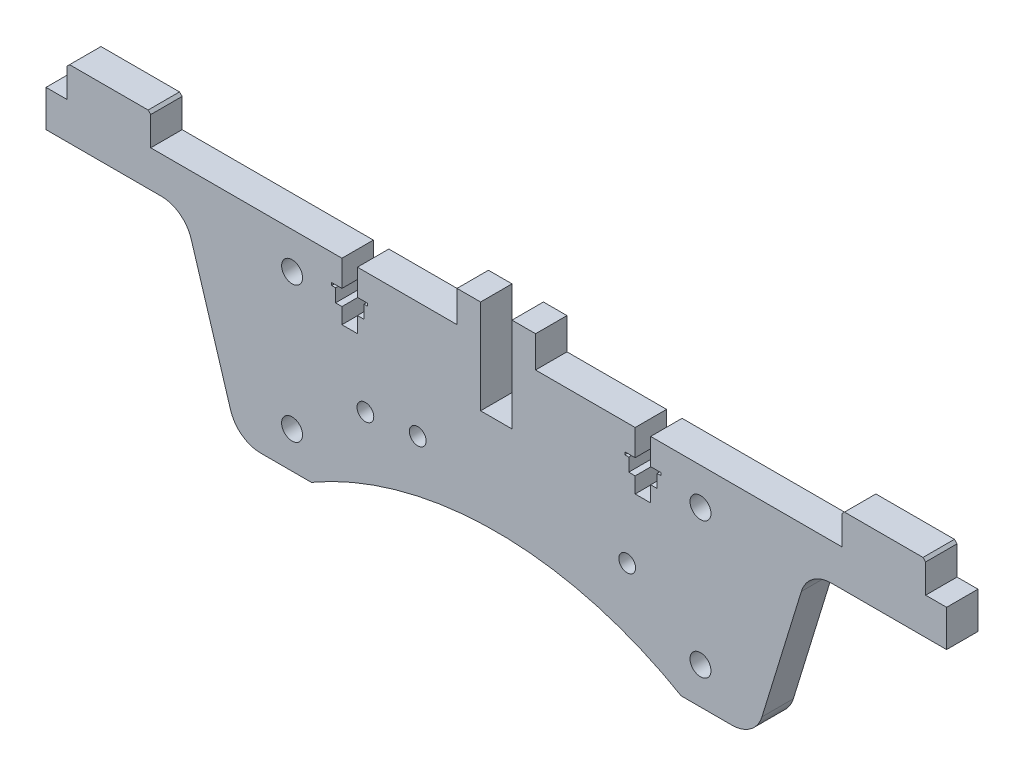
SolidWorks part; units mm, degrees
material "Oak"
ref_plane "Front Plane" through (0, 0, 0) normal (0, 0, 1) x (1, 0, 0)
ref_plane "Top Plane" through (0, 0, 0) normal (0, 1, 0) x (1, 0, 0)
ref_plane "Right Plane" through (0, 0, 0) normal (1, 0, 0) x (0, 0, -1)
sketch "Sketch1" plane through (0, 0, 0) normal (0, 0, 1) x (1, 0, 0)
  line L0 (0, -43.0686) -> (0, 56.6488) construction
  line L1 (-7.5, 20) -> (-66, 20)
  line L2 (49, 10.5) -> (65, 10.5) construction
  line L3 (49, 10.5) -> (49, -10.5) construction
  line L4 (49, -10.5) -> (65, -10.5) construction
  line L5 (65, 10.5) -> (65, -10.5) construction
  line L6 (66, 20) -> (66, 26)
  line L7 (66, 26) -> (82, 26)
  line L8 (86, 20) -> (86, 13)
  line L9 (-7.5, 20) -> (-7.5, 26)
  line L10 (35.3214, -20) -> (45, -20)
  line L11 (49, 10.5) -> (65, -10.5) construction
  line L12 (65, 10.5) -> (49, -10.5) construction
  line L13 (-65, 10.5) -> (-49, -10.5) construction
  line L14 (-49, 10.5) -> (-65, -10.5) construction
  line L15 (-65, 10.5) -> (-65, -10.5) construction
  line L16 (-49, -10.5) -> (-65, -10.5) construction
  line L17 (-49, 10.5) -> (-49, -10.5) construction
  line L18 (-49, 10.5) -> (-65, 10.5) construction
  line L19 (-7.5, 26) -> (-3, 26)
  line L20 (-64, 13) -> (-86, 13)
  line L21 (-82, 20) -> (-82, 26)
  line L22 (-86, 20) -> (-82, 20)
  line L23 (7.5, 20) -> (7.5, 26)
  line L24 (7.5, 26) -> (3, 26)
  line L25 (7.5, 20) -> (66, 20)
  line L26 (86, 20) -> (82, 20)
  line L27 (3, 26) -> (3, 8)
  line L28 (-57, 0) -> (57, 0) construction
  line L29 (3, 8) -> (-3, 8)
  line L30 (82, 20) -> (82, 26)
  line L31 (-86, 20) -> (-86, 13)
  line L32 (-66, 26) -> (-82, 26)
  line L33 (-35.3214, -20) -> (-45, -20)
  line L34 (-66, 20) -> (-66, 26)
  line L35 (-3, 26) -> (-3, 8)
  line L36 (-50.7358, -15.7609) -> (-58.2642, 8.7609)
  line L37 (50.7358, -15.7609) -> (58.2642, 8.7609)
  line L38 (64, 13) -> (86, 13)
  arc A0 (35.3214, -20) -> (-35.3214, -20) centre (0, -80.9132) ccw
  arc A1 (50.7358, -15.7609) -> (45, -20) centre (45, -14) cw
  arc A2 (58.2642, 8.7609) -> (64, 13) centre (64, 7) cw
  arc A6 (-58.2642, 8.7609) -> (-64, 13) centre (-64, 7) ccw
  arc A7 (-50.7358, -15.7609) -> (-45, -20) centre (-45, -14) ccw
  point P7 (-57, 0)
  point P9 (57, 0)
  point P20 (0, 0)
  point P24 (0, 40)
  point P25 (0, -10.5)
  point P27 (73.331, 42)
  point P30 (0, 40)
  point P31 (68.331, 20)
  point P32 (99.8, 42)
  point P38 (98.8347, 49.7973)
  point P54 (0, 8)
  dimension "D15" = 6
  dimension "D17" = 6
  dimension "D1" = 16
  dimension "D2" = 65
  dimension "D10" = 6
  dimension "D13" = 6
  dimension "D5" = 15
  dimension "D12" = 20
  dimension "D16" = 20
  dimension "D7" = 21
  dimension "D8" = 7
  dimension "D3" = 86
  dimension "D4" = 4
  dimension "D11" = 20
  dimension "D6" = 12
  dimension "D9" = 90
  dimension "D14" = 128
extrude "Boss-Extrude1" add sketch "Sketch1" along normal blind 6
sketch "Sketch2" plane through (0, 0, 6) normal (0, 0, 1) x (1, 0, 0)
  line L0 (0, 0) -> (0, -20) construction
  line L1 (-45, -20) -> (-35.3214, -20) construction
  line L2 (-25, -3.2) -> (25, -3.2) construction
  line L3 (0, 0) -> (0, -3.2) construction
  line L4 (66, 20) -> (7.5, 20) construction
  line L7 (31, -8) -> (31, 8) construction
  line L8 (31, -8) -> (47, -8) construction
  line L9 (31, 8) -> (47, 8) construction
  line L10 (47, -8) -> (47, 8) construction
  line L11 (31, -8) -> (47, 8) construction
  line L12 (31, 8) -> (47, -8) construction
  circle A0 centre (39, -13) radius 2
  circle A1 centre (39, 13) radius 2
  circle A2 centre (25, -3.2) radius 1.6
  circle A3 centre (-25, -3.2) radius 1.6
  point P7 (39, 0)
  dimension "D2" = 4
  dimension "D5" = 3.2
  dimension "D1" = 39
  dimension "D7" = 16
  dimension "D4" = 13
  dimension "D16" = 13
  dimension "D6" = 50
  dimension "D8" = 3.2
  dimension "D3" = 20
extrude "Cut-Extrude1" cut sketch "Sketch2" against normal through all
mirror "Mirror1" about plane through (0, 0, 0) normal (1, 0, 0) of "Cut-Extrude1"
chamfer "Chamfer1" distance 0.5 angle 45 4 edges at (66, 26, 3) (82, 26, 3) (-66, 26, 3) (-82, 26, 3)
sketch "Sketch4" plane through (0, 0, 6) normal (0, 0, 1) x (1, 0, 0)
  line L0 (0, 0) -> (0, 22.5154) construction
  line L1 (-28, 20) -> (-28, 9) construction
  line L2 (-7.5, 20) -> (-66, 20) construction
  line L3 (-29.48, 20) -> (-29.48, 15)
  line L4 (-29.48, 15) -> (-31.45, 15)
  line L5 (-31.45, 15) -> (-31.45, 14.5)
  line L6 (-31.45, 14.5) -> (-30.7, 14.5)
  line L7 (-30.7, 14.5) -> (-30.7, 12)
  line L8 (-30.7, 12) -> (-29.48, 12)
  line L9 (-29.48, 12) -> (-29.48, 9)
  line L10 (-29.48, 9) -> (-26.52, 9)
  line L11 (-26.52, 12) -> (-26.52, 9)
  line L12 (-25.3, 12) -> (-26.52, 12)
  line L13 (-25.3, 14.5) -> (-25.3, 12)
  line L14 (-24.55, 14.5) -> (-25.3, 14.5)
  line L15 (-24.55, 15) -> (-24.55, 14.5)
  line L16 (-26.52, 15) -> (-24.55, 15)
  line L17 (-26.52, 20) -> (-26.52, 15)
  line L18 (28, 20) -> (28, 9) construction
  line L19 (26.52, 20) -> (26.52, 15)
  line L20 (26.52, 15) -> (24.55, 15)
  line L21 (24.55, 15) -> (24.55, 14.5)
  line L22 (24.55, 14.5) -> (25.3, 14.5)
  line L23 (25.3, 14.5) -> (25.3, 12)
  line L24 (25.3, 12) -> (26.52, 12)
  line L25 (26.52, 12) -> (26.52, 9)
  line L26 (29.48, 9) -> (26.52, 9)
  line L27 (29.48, 12) -> (29.48, 9)
  line L28 (30.7, 12) -> (29.48, 12)
  line L29 (30.7, 14.5) -> (30.7, 12)
  line L30 (31.45, 14.5) -> (30.7, 14.5)
  line L31 (31.45, 15) -> (31.45, 14.5)
  line L32 (29.48, 15) -> (31.45, 15)
  line L33 (29.48, 20) -> (29.48, 15)
  line L34 (-29.48, 20) -> (-26.52, 20)
  line L35 (26.52, 20) -> (29.48, 20)
  dimension "D1" = 0.5
  dimension "D2" = 2.5
  dimension "D3" = 3
  dimension "D4" = 11
  dimension "D5" = 2.96
  dimension "D6" = 6.9
  dimension "D7" = 5.4
  dimension "D8" = 28
extrude "Cut-Extrude2" cut sketch "Sketch4" against normal through all
sketch "Sketch5" plane through (0, 0, 6) normal (0, 0, 1) x (1, 0, 0)
  circle A0 centre (-15, -2.2) radius 1.6
  circle A1 centre (-25, -3.2) radius 1.6 construction
  point P2 (-25, -3.2)
  dimension "D1" = 10
  dimension "D2" = 1
extrude "Cut-Extrude3" cut sketch "Sketch5" against normal through all
equation "\"bed-plate-thickness\"=6"
equation "\"D1@Boss-Extrude1\"=\"y-rib-thickness\""
equation "\"D10@Sketch1\"=\"bed-plate-thickness\""
equation "\"D13@Sketch1\"=\"y-cross-rib-thickness\""
equation "\"y-cross-rib-thickness\"=6"
equation "\"y-rib-thickness\"=6"
equation "\"x-plate-thickness\"=5"
equation "\"rod-diameter\"=12"
equation "\"t-nut-hole-diameter\"=3"
equation "\"y-plate-thickness\"=5"
equation "\"D8@Sketch2\"=9-(11.6/2)"
